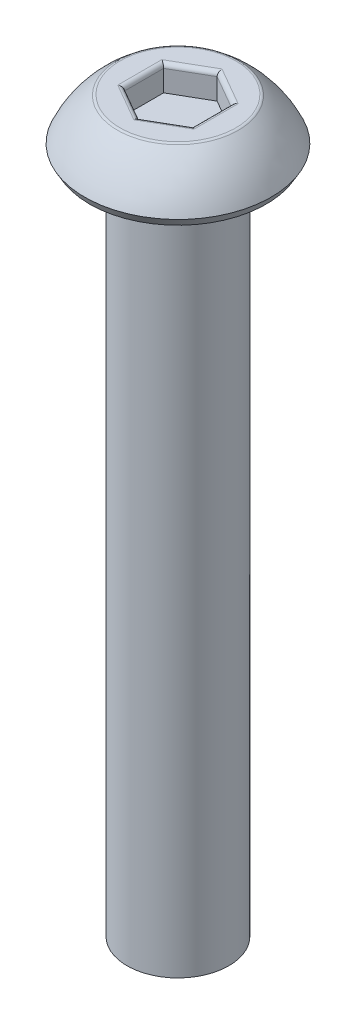
SolidWorks part; units mm, degrees
ref_plane "Front Plane" through (0, 0, 0) normal (0, 0, 1) x (1, 0, 0)
ref_plane "Top Plane" through (0, 0, 0) normal (0, 1, 0) x (1, 0, 0)
ref_plane "Right Plane" through (0, 0, 0) normal (1, 0, 0) x (0, 0, -1)
sketch "Sketch1" plane through (0, 0, 0) normal (1, 0, 0) x (0, 0, -1)
  line L0 (0, 0) -> (0, 1.5) construction
  line L1 (0, 1.5) -> (-1.75, 1.5)
  line L3 (-2.75, 0.25) -> (-2.6057, 0)
  line L4 (-2.6057, 0) -> (-1.5, 0)
  line L5 (-1.5, 0) -> (-1.5, -20)
  line L6 (-1.5, -20) -> (0, -20)
  line L7 (0, -20) -> (0, 1.5)
  line L8 (0, 0) -> (-1.5, 0) construction
  arc A0 (-1.75, 1.5) -> (-2.75, 0.25) centre (0.0077, -0.9312) ccw
  dimension "D5" = 3
  dimension "D1" = 1.5
  dimension "D2" = 2.75
  dimension "D3" = 1.75
  dimension "D4" = 0.25
  dimension "D6" = 60
  dimension "D7" = 1.5
  dimension "D8" = 20
revolve "Revolve1" add sketch "Sketch1" angle 360 about L7
sketch "Sketch2" plane through (0, 1.5, 0) normal (0, 1, 0) x (1, 0, 0)
  line L1 (0, 1.1547) -> (-1, 0.5774)
  line L2 (-1, 0.5774) -> (-1, -0.5774)
  line L3 (-1, -0.5774) -> (0, -1.1547)
  line L4 (0, -1.1547) -> (1, -0.5774)
  line L5 (1, -0.5774) -> (1, 0.5774)
  line L6 (1, 0.5774) -> (0, 1.1547)
  circle A0 centre (0, 0) radius 1 construction
  dimension "D1" = 2
extrude "Cut-Extrude1" cut sketch "Sketch2" against normal blind 0.75
fillet "Fillet1" radius 0.125 7 edges at (0, 1.5, -1.75) (-0.5, 1.5, 0.866) (0.5, 1.5, 0.866) (1, 1.5, 0) (0.5, 1.5, -0.866) (-0.5, 1.5, -0.866) (-1, 1.5, 0)
